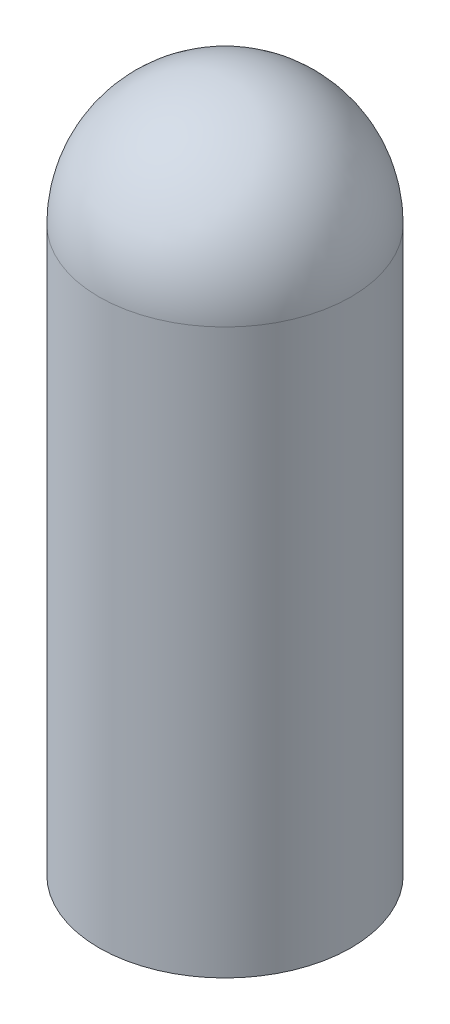
SolidWorks part; units mm, degrees
material "Glass"
ref_plane "Front Plane" through (0, 0, 0) normal (0, 0, 1) x (1, 0, 0)
ref_plane "Top Plane" through (0, 0, 0) normal (0, 1, 0) x (1, 0, 0)
ref_plane "Right Plane" through (0, 0, 0) normal (1, 0, 0) x (0, 0, -1)
sketch "Sketch1" plane through (0, 0, 0) normal (0, 0, 1) x (1, 0, 0)
  line L0 (0, 42.5) -> (0, 52)
  line L1 (0, 0) -> (-9.5, 0)
  line L2 (0, 0) -> (0, 42.5)
  line L4 (-9.5, 0) -> (-9.5, 42.5)
  arc A0 (-9.5, 42.5) -> (0, 52) centre (0, 42.5) cw
  dimension "D3" = 9.5
  dimension "D1" = 9.5
  dimension "D2" = 42.5
revolve "Revolve6" add sketch "Sketch1" angle 360 about L0
shell "Shell1" thickness 1.5
